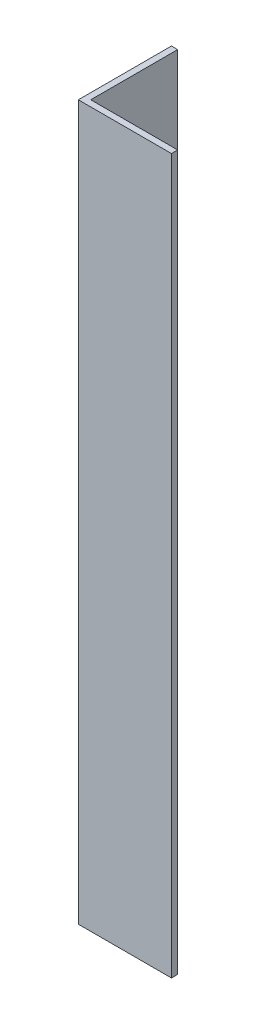
SolidWorks part; units mm, degrees
material "1060 Сплав"
ref_plane "Спереди" through (0, 0, 0) normal (0, 0, 1) x (1, 0, 0)
ref_plane "Сверху" through (0, 0, 0) normal (0, 1, 0) x (1, 0, 0)
ref_plane "Справа" through (0, 0, 0) normal (1, 0, 0) x (0, 0, -1)
sketch "Эскиз1" plane through (0, 0, 0) normal (0, 1, 0) x (1, 0, 0)
  line L0 (0, 0) -> (0, 15)
  line L1 (0, 15) -> (1, 15)
  line L2 (1, 15) -> (1, 1)
  line L3 (1, 1) -> (15, 1)
  line L4 (15, 1) -> (15, 0)
  line L5 (15, 0) -> (0, 0)
  dimension "D1" = 1
  dimension "D2" = 15
extrude "Бобышка-Вытянуть1" add sketch "Эскиз1" along normal blind 115
